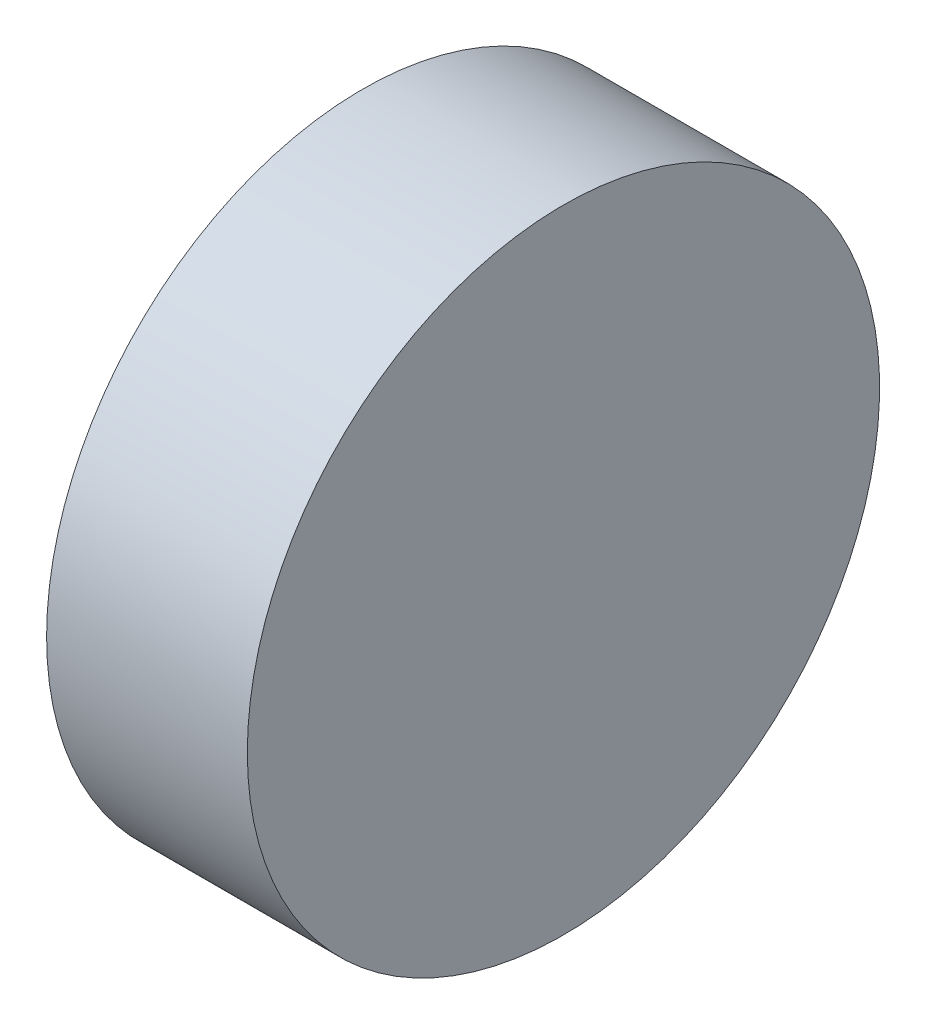
SolidWorks part; units mm, degrees
ref_plane "前视基准面" through (0, 0, 0) normal (0, 0, 1) x (1, 0, 0)
ref_plane "上视基准面" through (0, 0, 0) normal (0, 1, 0) x (1, 0, 0)
ref_plane "右视基准面" through (0, 0, 0) normal (1, 0, 0) x (0, 0, -1)
sketch "草图1" plane through (0, 0, 0) normal (0, 0, 1) x (1, 0, 0)
  line L0 (50.8002, 15.4586) -> (55.2877, 15.4586) construction
  line L1 (51.888, 15.4586) -> (51.888, 18.6086)
  line L2 (51.888, 18.6086) -> (53.888, 18.6086)
  line L3 (53.888, 18.6086) -> (53.888, 15.4586)
  line L4 (51.888, 15.4586) -> (53.888, 15.4586)
  dimension "D1" = 2
  dimension "D2" = 3.15
revolve "旋转1" add sketch "草图1" angle 360 about L0
